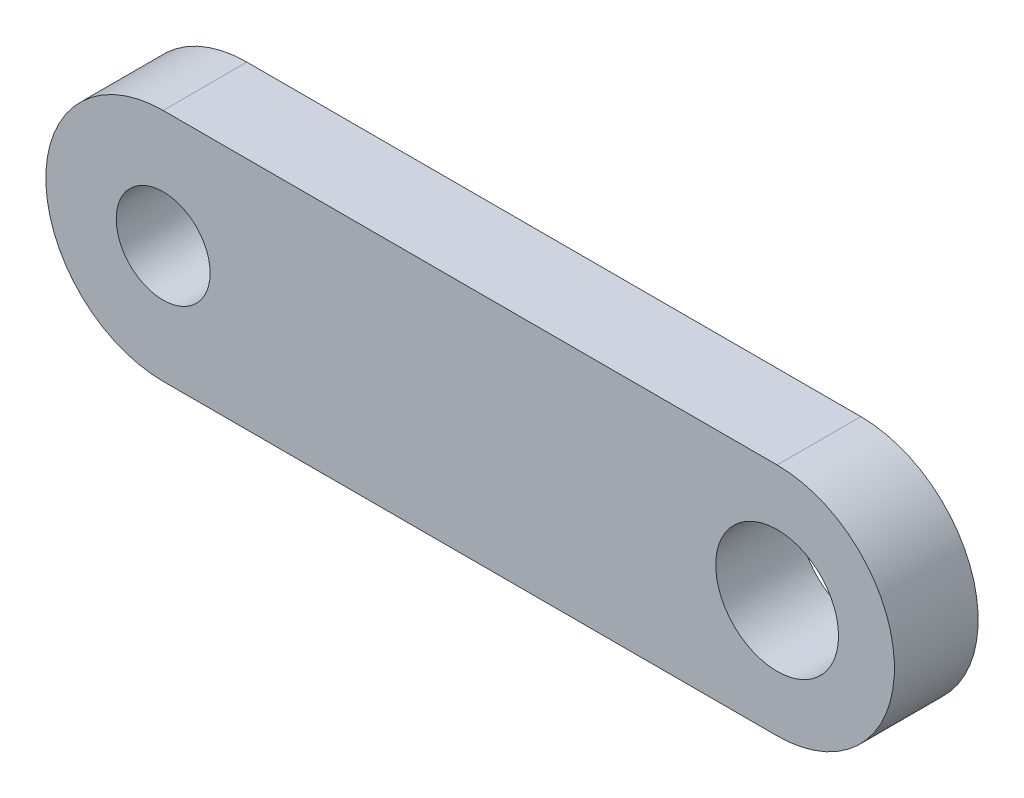
SolidWorks part; units mm, degrees
ref_plane "Front Plane" through (0, 0, 0) normal (0, 0, 1) x (1, 0, 0)
ref_plane "Top Plane" through (0, 0, 0) normal (0, 1, 0) x (1, 0, 0)
ref_plane "Right Plane" through (0, 0, 0) normal (1, 0, 0) x (0, 0, -1)
sketch "Model" plane through (0, 0, 0) normal (0, 0, 1) x (1, 0, 0)
  line L0 (64.0514, 50.1492) -> (78.9995, 50.1492)
  line L1 (78.9995, 50.1492) -> (80.882, 50.1492)
  line L2 (58.882, 58.5567) -> (80.882, 58.5567)
  line L3 (58.882, 50.1492) -> (64.0514, 50.1492)
  circle A0 centre (80.882, 54.3522) radius 2.2
  circle A1 centre (58.882, 54.3529) radius 1.6824
  arc A2 (58.882, 58.5567) -> (58.882, 50.1492) centre (58.882, 54.3529) ccw
  arc A3 (80.882, 50.1492) -> (80.882, 58.5567) centre (80.882, 54.3529) ccw
  dimension "D1" = 22
extrude "Boss-Extrude1" add sketch "Model" along normal blind 3
